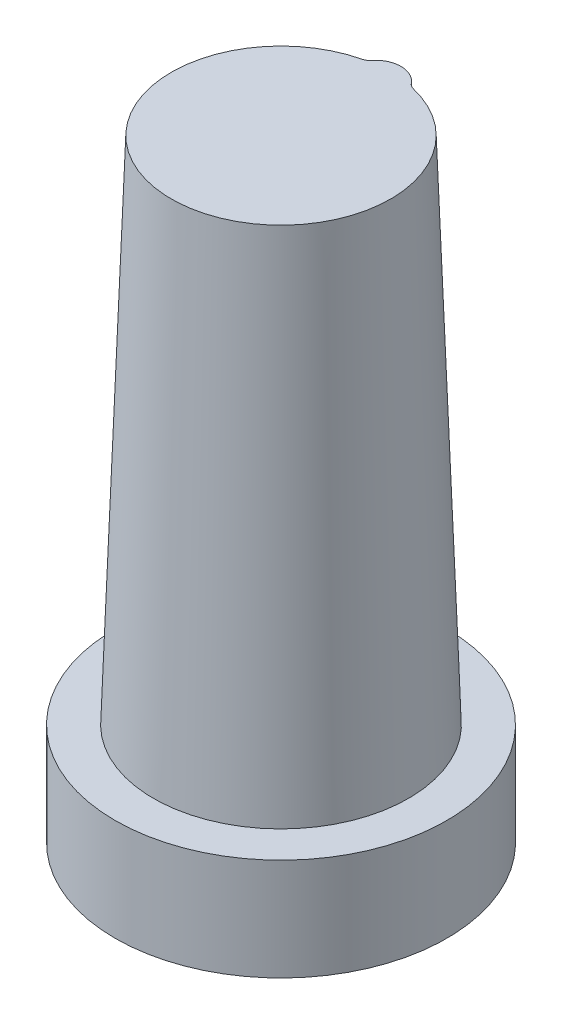
SolidWorks part; units mm, degrees
ref_plane "Vorne" through (0, 0, 0) normal (0, 0, 1) x (1, 0, 0)
ref_plane "Oben" through (0, 0, 0) normal (0, 1, 0) x (1, 0, 0)
ref_plane "Rechts" through (0, 0, 0) normal (1, 0, 0) x (0, 0, -1)
sketch3d "3D-Skizze1"
  line L0 (0, 0, 0) -> (0, 20, 0) construction
  line L1 (0, 0, 0) -> (20, 0, 0) construction
  line L2 (0, 0, 0) -> (0, 0, 20) construction
sketch "Skizze1" plane through (0, 0, 0) normal (0, 1, 0) x (1, 0, 0)
  circle A0 centre (0, 0) radius 25
  dimension "D1" = 50
extrude "Aufsatz-Linear austragen1" add sketch "Skizze1" along normal blind 100
sketch "Skizze2" plane through (0, 0, 0) normal (0, -1, 0) x (1, 0, 0)
  circle A0 centre (0, 0) radius 32.5
  dimension "D1" = 65
extrude "Aufsatz-Linear austragen2" add sketch "Skizze2" along normal blind 20
draft "Formschräge1" type of draft neutral plane draft angle 2 faces to draft 1 face at (0, 100, 25) neutral plane through (0, 0, 0) neutral plane normal (0, 1, 0) parameters "D1"=2
sketch "Skizze6" plane through (0, 0, 0) normal (1, 0, 0) x (0, 0, -1)
  line L0 (21.5079, 100) -> (25, 0)
sketch "Skizze8" plane through (0, 100, 0) normal (0, 1, 0) x (1, 0, 0)
  line L0 (0, 0) -> (0, 18.5079) construction
  line L1 (0, 18.5079) -> (0, 21.5079) construction
  arc A0 (4.2903, 21.0757) -> (-4.2903, 21.0757) centre (0, 18.5079) ccw
  circle A1 centre (0, 0) radius 21.5079 construction
  arc A2 (4.2903, 21.0757) -> (-4.2903, 21.0757) centre (0, 0) ccw
  dimension "D1" = 10
  dimension "D2" = 3
sweep "Austragung6" add profiles "Skizze8" path "Skizze6"
fillet "Verrundung1" radius 2 2 edges at (-4.2855, 90.0185, -21.4322) (4.2677, 49.9076, -22.8623)
